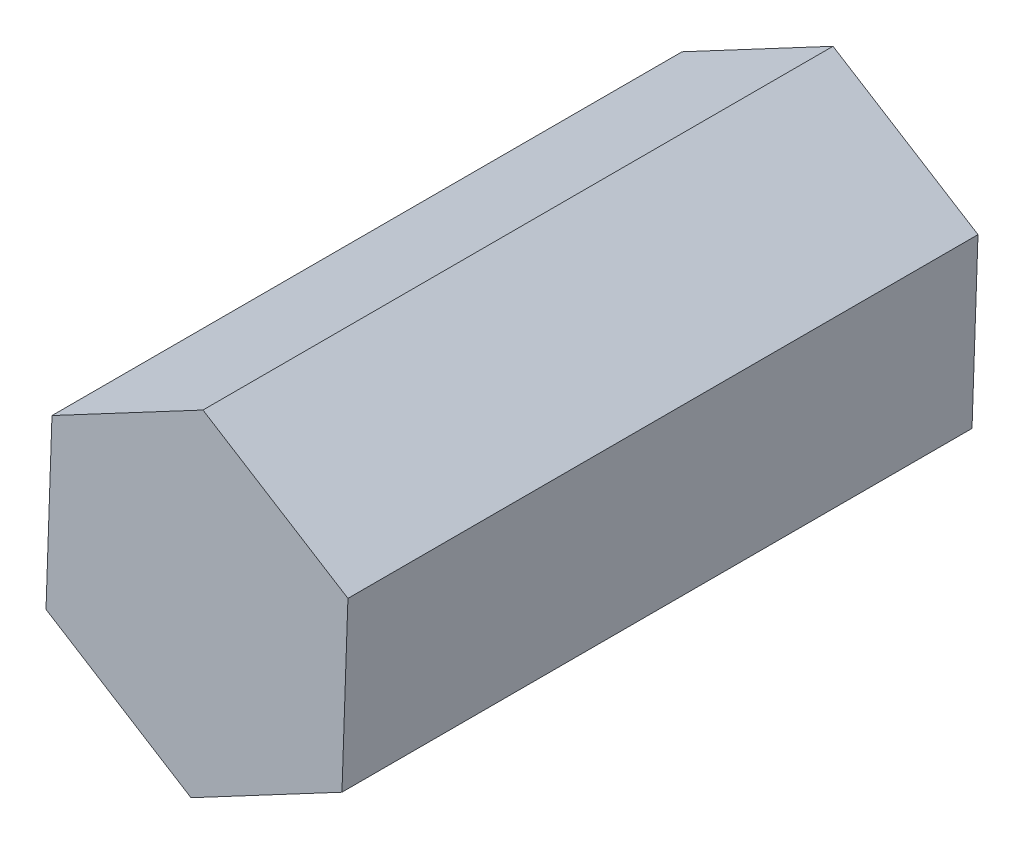
SolidWorks part; units mm, degrees
ref_plane "Front Plane" through (0, 0, 0) normal (0, 0, 1) x (1, 0, 0)
ref_plane "Top Plane" through (0, 0, 0) normal (0, 1, 0) x (1, 0, 0)
ref_plane "Right Plane" through (0, 0, 0) normal (1, 0, 0) x (0, 0, -1)
sketch "Sketch1" plane through (0, 0, 0) normal (0, 0, 1) x (1, 0, 0)
  line L1 (2.3011, -1.4382) -> (2.396, 1.2737)
  line L2 (2.396, 1.2737) -> (0.095, 2.7119)
  line L3 (0.095, 2.7119) -> (-2.3011, 1.4382)
  line L4 (-2.3011, 1.4382) -> (-2.396, -1.2737)
  line L5 (-2.396, -1.2737) -> (-0.095, -2.7119)
  line L6 (-0.095, -2.7119) -> (2.3011, -1.4382)
  circle A0 centre (0, 0) radius 2.35 construction
  dimension "D1" = 4.7
extrude "Boss-Extrude1" add sketch "Sketch1" along normal blind 10
sketch "Sketch2" plane through (0, 0, 0) normal (0, 0, 1) x (1, 0, 0)
  circle A0 centre (0, 0) radius 1.25
extrude "Cut-Extrude1" cut sketch "Sketch2" along normal blind 5
